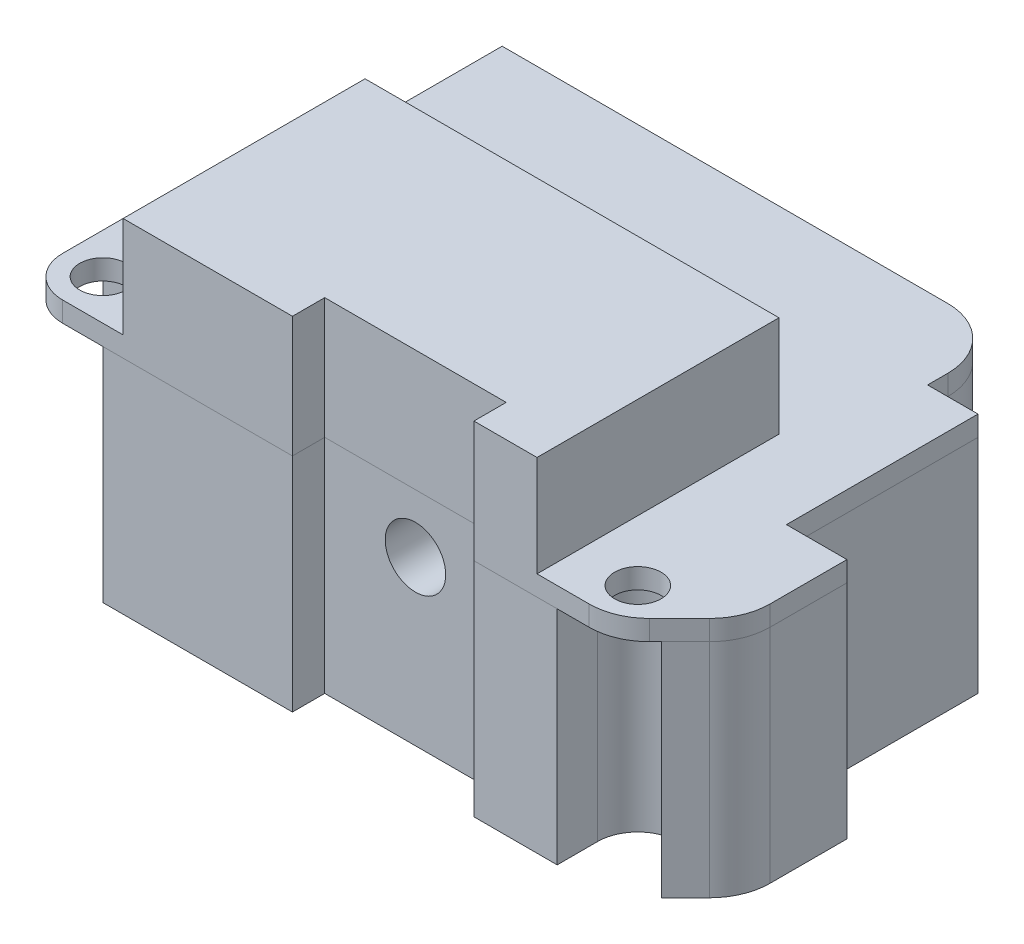
SolidWorks part; units mm, degrees
ref_plane "前视基准面" through (0, 0, 0) normal (0, 0, 1) x (1, 0, 0)
ref_plane "上视基准面" through (0, 0, 0) normal (0, 1, 0) x (1, 0, 0)
ref_plane "右视基准面" through (0, 0, 0) normal (1, 0, 0) x (0, 0, -1)
sketch "草图1" plane through (0, 0, 0) normal (0, 1, 0) x (1, 0, 0)
  line L0 (-14.3, 8.9) -> (-14.3, 12.9)
  line L1 (-16.3, 8.9) -> (-14.3, 8.9) construction
  line L2 (-16.3, 1.4) -> (-16.3, -6.9)
  line L3 (-14.3, -8.9) -> (11.8151, -8.9)
  line L4 (16.3, -0.6) -> (16.3, -4.4151)
  line L5 (-16.3, 8.9) -> (16.3, -8.9) construction
  line L6 (-16.3, -8.9) -> (16.3, 8.9) construction
  line L7 (-14.3, 12.9) -> (7.8, 12.9)
  line L8 (10.8, 9.9) -> (10.8, 8.9)
  line L9 (13.9364, -8.0213) -> (15.4213, -6.5364)
  line L10 (10.8, 8.9) -> (13.3, 8.9)
  line L11 (-14.3, 8.9) -> (-14.3, 1.4)
  line L12 (-14.3, 1.4) -> (-16.3, 1.4)
  line L13 (13.3, 8.9) -> (13.3, -0.6)
  line L14 (13.3, -0.6) -> (16.3, -0.6)
  line L15 (-16.3, 8.9) -> (-16.3, 1.4) construction
  line L16 (13.3, 8.9) -> (16.3, 8.9) construction
  line L17 (16.3, 8.9) -> (16.3, -0.6) construction
  line L18 (-14.3, -6.9) -> (12.2293, -6.9) construction
  arc A0 (13.9364, -8.0213) -> (11.8151, -8.9) centre (11.8151, -5.9) cw
  arc A1 (15.4213, -6.5364) -> (16.3, -4.4151) centre (13.3, -4.4151) ccw
  arc A2 (7.8, 12.9) -> (10.8, 9.9) centre (7.8, 9.9) cw
  arc A3 (-16.3, -6.9) -> (-14.3, -8.9) centre (-14.3, -6.9) ccw
  circle A4 centre (-14.3, -6.9) radius 1.15
  circle A5 centre (12.2293, -6.9) radius 1.15
  point P0 (0, 0)
  point P14 (13.0577, -8.9)
  dimension "D7" = 3
  dimension "D10" = 3
  dimension "D13" = 2
  dimension "D14" = 2.3
  dimension "D15" = 2
  dimension "D1" = 32.6
  dimension "D2" = 17.8
  dimension "D3" = 2
  dimension "D4" = 4
  dimension "D5" = 5.5
  dimension "D6" = 45
  dimension "D8" = 2.1
  dimension "D9" = 7.5
  dimension "D11" = 9.5
  dimension "D12" = 3
extrude "凸台-拉伸1" add sketch "草图1" along normal blind 1
sketch "草图2" plane through (0, 0, 0) normal (0, 1, 0) x (1, 0, 0)
  line L27 (-14.3, -8.9) -> (11.8151, -8.9)
  line L28 (-16.3, 1.4) -> (-16.3, -6.9)
  line L29 (-14.3, 1.4) -> (-16.3, 1.4)
  line L30 (-14.3, 12.9) -> (-14.3, 1.4)
  line L31 (7.8, 12.9) -> (-14.3, 12.9)
  line L32 (10.8, 8.9) -> (10.8, 9.9)
  line L33 (13.3, 8.9) -> (10.8, 8.9)
  line L34 (13.3, -0.6) -> (13.3, 8.9)
  line L35 (16.3, -0.6) -> (13.3, -0.6)
  line L36 (16.3, -4.4151) -> (16.3, -0.6)
  line L37 (13.9364, -8.0213) -> (15.4213, -6.5364)
  line L38 (-14.3, -8.9) -> (11.8151, -8.9)
  line L39 (-16.3, 1.4) -> (-16.3, -6.9)
  line L40 (-14.3, 1.4) -> (-16.3, 1.4)
  line L41 (-14.3, 12.9) -> (-14.3, 1.4)
  line L42 (7.8, 12.9) -> (-14.3, 12.9)
  line L43 (10.8, 8.9) -> (10.8, 9.9)
  line L44 (13.3, 8.9) -> (10.8, 8.9)
  line L45 (13.3, -0.6) -> (13.3, 8.9)
  line L46 (16.3, -0.6) -> (13.3, -0.6)
  line L47 (16.3, -4.4151) -> (16.3, -0.6)
  line L48 (13.9364, -8.0213) -> (15.4213, -6.5364)
  arc A6 (10.8, 9.9) -> (7.8, 12.9) centre (7.8, 9.9) ccw
  arc A7 (15.4213, -6.5364) -> (16.3, -4.4151) centre (13.3, -4.4151) ccw
  arc A8 (11.8151, -8.9) -> (13.9364, -8.0213) centre (11.8151, -5.9) ccw
  arc A9 (10.8, 9.9) -> (7.8, 12.9) centre (7.8, 9.9) ccw
  arc A10 (15.4213, -6.5364) -> (16.3, -4.4151) centre (13.3, -4.4151) ccw
  arc A11 (11.8151, -8.9) -> (13.9364, -8.0213) centre (11.8151, -5.9) ccw
  arc A13 (-16.3, -6.9) -> (-14.3, -8.9) centre (-14.3, -6.9) ccw
  arc A14 (-16.3, -6.9) -> (-14.3, -8.9) centre (-14.3, -6.9) ccw
  dimension "D1" = 0
extrude "凸台-拉伸2" add sketch "草图2" against normal offset from surface (11 mm away) 11 separate body up to face at (-14.3, 0, 8.05) offset beyond the face yes
sketch "草图4" plane through (0, -11, 0) normal (0, -1, 0) x (1, 0, 0)
  line L0 (10.2293, 6.9) -> (10.2293, 8.9)
  line L1 (11.8151, 8.9) -> (-14.3, 8.9) construction
  line L2 (10.2293, 8.9) -> (14.2293, 8.9)
  line L3 (14.2293, 8.9) -> (14.2293, 6.9)
  line L4 (-16.3, 4.9) -> (-14.3, 4.9)
  line L5 (-16.3, 6.9) -> (-16.3, -1.4) construction
  line L7 (-12.3, 6.9) -> (-12.3, 8.9)
  line L8 (-12.3, 8.9) -> (-16.3, 8.9)
  line L9 (-16.3, 8.9) -> (-16.3, 6.9)
  arc A0 (-14.3, 4.9) -> (-12.3, 6.9) centre (-14.3, 6.9) ccw
  arc A1 (10.2293, 6.9) -> (14.2293, 6.9) centre (12.2293, 6.9) ccw
  arc M1 (13.9364, 8.0213) -> (11.8151, 8.9) centre (11.8151, 5.9) ccw
  line M2 (11.8151, 8.9) -> (-14.3, 8.9)
  arc M3 (-14.3, 8.9) -> (-16.3, 6.9) centre (-14.3, 6.9) ccw
  line M4 (-16.3, 6.9) -> (-16.3, -1.4)
  line M15 (15.4213, 6.5364) -> (13.9364, 8.0213)
extrude "切除-拉伸1" cut sketch "草图4" against normal blind 11 contours L4 A0 L7 M2 M3 M4 | L0 A1 L3 M15 M1 M2
sketch "草图5" plane through (0, 1, 0) normal (0, 1, 0) x (1, 0, 0)
  line L0 (-14.3, -8.9) -> (11.8151, -8.9) construction
  line L1 (-11.3, 3.1) -> (9.2293, 3.1)
  line L2 (-11.3, 3.1) -> (-11.3, -8.9)
  line L3 (-11.3, -8.9) -> (9.2293, -8.9)
  line L4 (9.2293, 3.1) -> (9.2293, -8.9)
  line L5 (-11.3, 3.1) -> (9.2293, -8.9) construction
  line L6 (-11.3, -8.9) -> (9.2293, 3.1) construction
  circle A0 centre (-14.3, -6.9) radius 1.15 construction
  circle A1 centre (12.2293, -6.9) radius 1.15 construction
  point P0 (-1.0354, -2.9)
  dimension "D2" = 3
  dimension "D1" = 12
  dimension "D3" = 3
extrude "凸台-拉伸3" add sketch "草图5" along normal blind 5
sketch "草图6" plane through (0, -11, 0) normal (0, -1, 0) x (1, 0, 0)
  line L0 (10.2293, 8.9) -> (-12.3, 8.9) construction
  line L1 (-2.9, 10.5) -> (6.1, 10.5)
  line L2 (-2.9, 10.5) -> (-2.9, 7.3)
  line L3 (-2.9, 7.3) -> (6.1, 7.3)
  line L4 (6.1, 10.5) -> (6.1, 7.3)
  line L5 (-2.9, 10.5) -> (6.1, 7.3) construction
  line L6 (-2.9, 7.3) -> (6.1, 10.5) construction
  line L7 (-16.3, 4.9) -> (-16.3, -1.4) construction
  point P0 (1.6, 8.9)
  dimension "D1" = 17.9
  dimension "D2" = 9
  dimension "D3" = 1.6
extrude "切除-拉伸2" cut sketch "草图6" against normal through all
sketch "草图7" plane through (0, 0, 7.3) normal (0, 0, 1) x (1, 0, 0)
  line L0 (-2.9, -2.9) -> (6.1, -2.9) construction
  line L1 (-2.9, 0) -> (-2.9, -11) construction
  line L2 (6.1, -11) -> (6.1, 0) construction
  line L4 (6.1, 6) -> (-2.9, 6) construction
  circle A0 centre (1.6, -2.9) radius 1.5
  dimension "D2" = 3
  dimension "D1" = 8.9
extrude "切除-拉伸3" cut sketch "草图7" against normal blind 4
